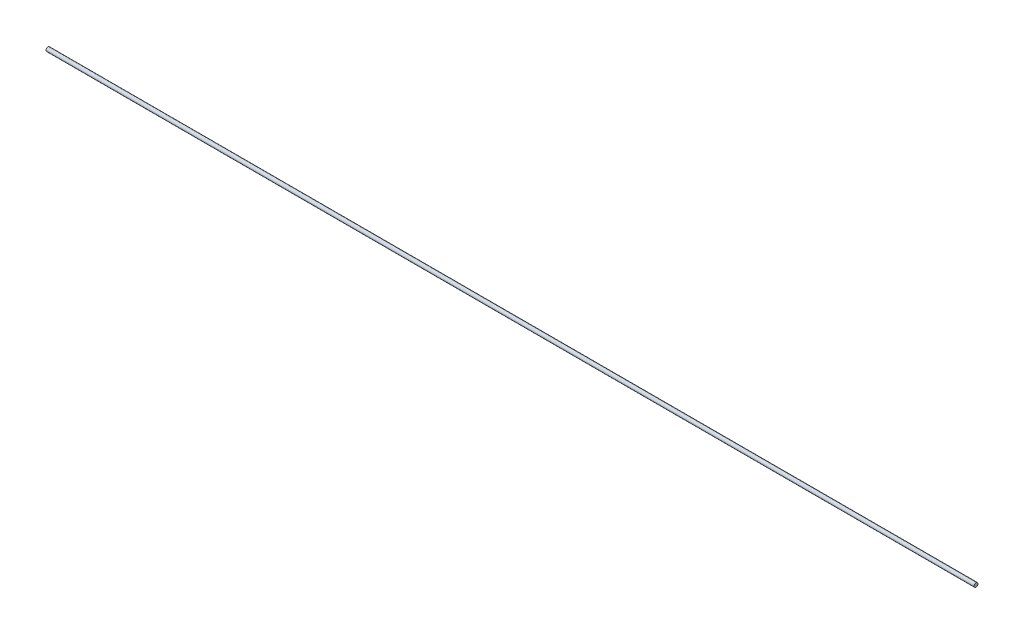
SolidWorks part; units mm, degrees
ref_plane "Front Plane" through (0, 0, 0) normal (0, 0, 1) x (1, 0, 0)
ref_plane "Top Plane" through (0, 0, 0) normal (0, 1, 0) x (1, 0, 0)
ref_plane "Right Plane" through (0, 0, 0) normal (1, 0, 0) x (0, 0, -1)
sketch "Sketch1" plane through (0, 0, 0) normal (1, 0, 0) x (0, 0, -1)
  circle A0 centre (0, 0) radius 0.635
  dimension "D1" = 1.27
extrude "Boss-Extrude1" add sketch "Sketch1" along normal blind 300
